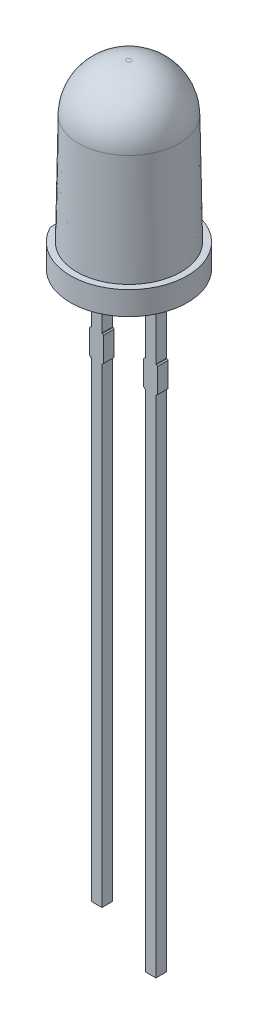
SolidWorks part; units mm, degrees
ref_plane "Front Plane" through (0, 0, 0) normal (0, 0, 1) x (1, 0, 0)
ref_plane "Top Plane" through (0, 0, 0) normal (0, 1, 0) x (1, 0, 0)
ref_plane "Right Plane" through (0, 0, 0) normal (1, 0, 0) x (0, 0, -1)
sketch "Sketch1" plane through (0, 0, 0) normal (0, 1, 0) x (1, 0, 0)
  circle A0 centre (0, 0) radius 2.75
  dimension "D1" = 5.5
extrude "Boss-Extrude1" add sketch "Sketch1" along normal blind 1.1 contours A0
sketch "Sketch2" plane through (0, 1.1, 0) normal (0, 1, 0) x (1, 0, 0)
  circle A0 centre (0, 0) radius 2.45
  dimension "D1" = 4.9
ref_plane "Plane1" through (0, 8.5, 0) normal (0, -1, 0) x (-1, 0, 0)
sketch "Sketch3" plane through (0, 0, 0) normal (0, 0, 1) x (1, 0, 0)
  line L0 (0, 1.1) -> (0, 8.5)
  line L2 (-3.025, 8.5) -> (3.025, 8.5) construction
  point P4 (0, 0)
  point P7 (0, 8.1421)
sweep "Sweep1" add profiles "Sketch2" path "Sketch3"
draft "Draft1" type of draft neutral plane draft angle 1 faces to draft 1 face at (0, 8.5, 2.45) neutral plane through (0, 1.1, 0) neutral plane normal (0, 1, 0) parameters "D1"=1
fillet "Fillet1" radius 2.25 1 edges at (0, 8.5, 2.3208)
sketch "Sketch5" plane through (0, 1.1, 0) normal (0, 1, 0) x (1, 0, 0)
  line L0 (-2.45, 1.249) -> (-2.45, -1.249)
  circle A1 centre (0, 0) radius 2.45 construction
  circle A2 centre (0, 0) radius 2.75 construction
  arc A3 (-2.45, 1.249) -> (-2.45, -1.249) centre (0, 0) ccw
extrude "Cut-Extrude1" cut sketch "Sketch5" against normal blind 1.1
sketch "Sketch6" plane through (0, 0, 0) normal (0, -1, 0) x (1, 0, 0)
  line L0 (-2.2943, 0) -> (2.578, 0) construction
  line L1 (-1.52, 0.25) -> (-1.02, 0.25)
  line L2 (-1.52, 0.25) -> (-1.52, -0.25)
  line L3 (-1.52, -0.25) -> (-1.02, -0.25)
  line L4 (-1.02, 0.25) -> (-1.02, -0.25)
  line L5 (-1.52, 0.25) -> (-1.02, -0.25) construction
  line L6 (-1.52, -0.25) -> (-1.02, 0.25) construction
  line L7 (1.02, 0.25) -> (1.52, 0.25)
  line L8 (1.02, 0.25) -> (1.02, -0.25)
  line L9 (1.02, -0.25) -> (1.52, -0.25)
  line L10 (1.52, 0.25) -> (1.52, -0.25)
  line L11 (1.02, 0.25) -> (1.52, -0.25) construction
  line L12 (1.02, -0.25) -> (1.52, 0.25) construction
  line L13 (0, 1.1407) -> (0, -1.4584) construction
  point P0 (-1.27, 0)
  point P5 (1.27, 0)
  point P15 (0, 0)
  dimension "D1" = 0.5
  dimension "D2" = 0.5
  dimension "D3" = 2.54
extrude "Boss-Extrude2" add sketch "Sketch6" along normal blind 28
other "Move Face1" face at (-1.27, -28, 0) parameters "D1"=1.6
sketch "Sketch7" plane through (0, 0, 0.25) normal (0, 0, 1) x (1, 0, 0)
  line L0 (1.52, -28) -> (1.02, -28) construction
  line L1 (0.945, -3) -> (1.595, -3)
  line L2 (0.945, -3) -> (0.945, -4.25)
  line L3 (0.945, -4.25) -> (1.595, -4.25)
  line L4 (1.595, -3) -> (1.595, -4.25)
  line L5 (-1.595, -3) -> (-0.945, -3)
  line L6 (-1.595, -3) -> (-1.595, -4.25)
  line L7 (-1.595, -4.25) -> (-0.945, -4.25)
  line L8 (-0.945, -3) -> (-0.945, -4.25)
  line L9 (1.27, 0) -> (1.27, -5.5864) construction
  line L10 (1.52, 0) -> (1.02, 0) construction
  line L11 (-1.27, 0) -> (-1.27, -8.0728) construction
  line L12 (-1.02, 0) -> (-1.52, 0) construction
  dimension "D1" = 25
  dimension "D2" = 23.75
  dimension "D3" = 0.65
extrude "Boss-Extrude3" add sketch "Sketch7" against normal up to surface (0.5 mm away) up to face at (1.27, -14, -0.25)
chamfer "Chamfer1" distance 0.05 angle 45 8 edges at (1.595, -4.25, 0) (1.595, -3, 0) (0.945, -3, 0) (0.945, -4.25, 0) (-0.945, -4.25, 0) (-0.945, -3, 0) (-1.595, -4.25, 0) (-1.595, -3, 0)
